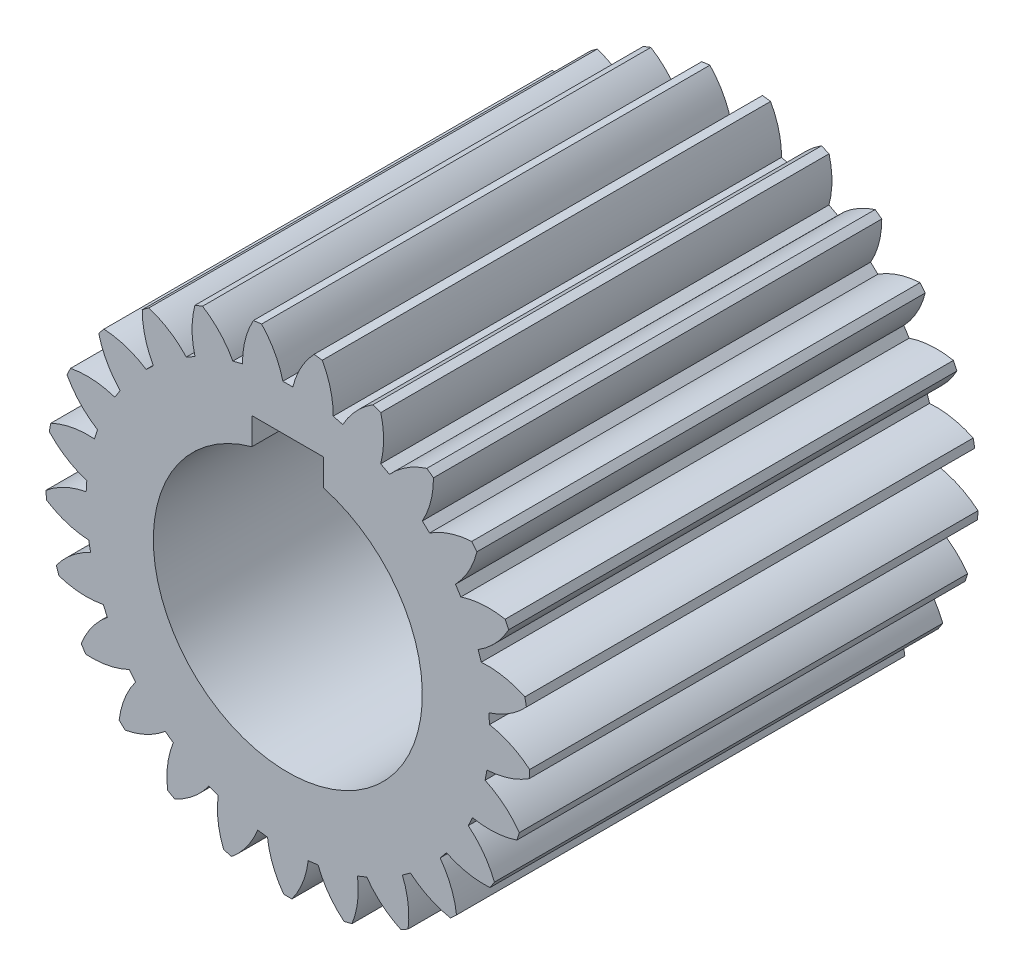
SolidWorks part; units mm, degrees
ref_plane "Front Plane" through (0, 0, 0) normal (0, 0, 1) x (1, 0, 0)
ref_plane "Top Plane" through (0, 0, 0) normal (0, 1, 0) x (1, 0, 0)
ref_plane "Right Plane" through (0, 0, 0) normal (1, 0, 0) x (0, 0, -1)
sketch "Sketch1" plane through (0, 0, 0) normal (0, 0, 1) x (1, 0, 0)
  circle A0 centre (0, 0) radius 25
  circle A1 centre (0, 0) radius 22.5
  circle A2 centre (0, 0) radius 27
  dimension "D1" = 54
  dimension "D2" = 50
  dimension "D3" = 45
extrude "Boss-Extrude1" add sketch "Sketch1" along normal blind 50 contours A2
sketch "Sketch3" plane through (0, 0, 50) normal (0, 0, 1) x (1, 0, 0)
  line L0 (0, 0) -> (0, -14.5028) construction
  line L1 (0, 0) -> (-2.4937, 39.6366) construction
  line L3 (3.0822, 27) -> (-3.0822, 27)
  line L4 (0.5546, 22.5) -> (-0.5546, 22.5)
  arc A0 (-0.5546, 22.5) -> (-3.0822, 27) centre (-9.981, 20.1651) ccw
  circle A1 centre (0, 0) radius 27 construction
  arc A2 (0.5546, 22.5) -> (3.0822, 27) centre (9.981, 20.1651) cw
  circle A5 centre (0, 0) radius 22.5 construction
  point P8 (0, 27)
  point P12 (0, 22.5)
  dimension "D1" = 3.6
extrude "Cut-Extrude1" cut sketch "Sketch3" against normal blind 50
pattern_circular "CirPattern1" count 25 over 360 about axis through (0, 0, 0) along (0, 0, 1) of "Cut-Extrude1"
sketch "Sketch4" plane through (0, 0, 50) normal (0, 0, 1) x (1, 0, 0)
  line L6 (-4, 14.4568) -> (-4, 17.4568)
  line L7 (-4, 17.4568) -> (4, 17.4568)
  line L8 (4, 14.4568) -> (4, 17.4568)
  arc A0 (-4, 14.4568) -> (4, 14.4568) centre (0, 0) ccw
  dimension "D1" = 30
  dimension "D2" = 3
  dimension "D3" = 8
  dimension "D4" = 4
extrude "Cut-Extrude2" cut sketch "Sketch4" against normal blind 50
equation "\"module\"= 2"
equation "\"teeth\"= 25"
equation "\"D1@Sketch1\"=\"module\"*(\"teeth\"+2)"
equation "\"D2@Sketch1\"=\"module\"*\"teeth\""
equation "\"D3@Sketch1\"=\"module\"*(\"teeth\"-2.5)"
equation "\"D1@Sketch3\"=360/(\"teeth\"*4)"
equation "\"D1@CirPattern1\"=\"teeth\""
